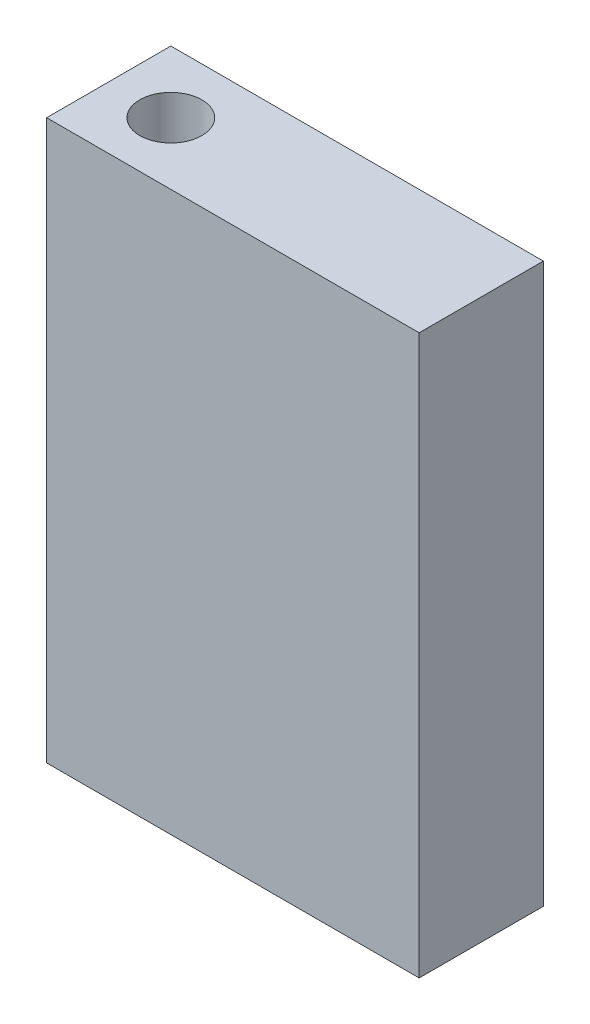
SolidWorks part; units mm, degrees
ref_plane "Front Plane" through (0, 0, 0) normal (0, 0, 1) x (1, 0, 0)
ref_plane "Top Plane" through (0, 0, 0) normal (0, 1, 0) x (1, 0, 0)
ref_plane "Right Plane" through (0, 0, 0) normal (1, 0, 0) x (0, 0, -1)
sketch "Sketch1" plane through (0, 0, 0) normal (0, 1, 0) x (1, 0, 0)
  line L1 (-23.0207, 17.3303) -> (6.9793, 17.3303)
  line L2 (-23.0207, 17.3303) -> (-23.0207, 27.3303)
  line L3 (-23.0207, 27.3303) -> (6.9793, 27.3303)
  line L4 (6.9793, 17.3303) -> (6.9793, 27.3303)
  dimension "D1" = 10
  dimension "D2" = 30
extrude "Boss-Extrude1" add sketch "Sketch1" along normal blind 45
sketch "Sketch2" plane through (0, 45, 0) normal (0, 1, 0) x (1, 0, 0)
  line L0 (6.9793, 17.3303) -> (6.9793, 27.3303) construction
  line L1 (6.9793, 27.3303) -> (-23.0207, 27.3303) construction
  circle A0 centre (-18.0207, 22.3303) radius 2.5
  dimension "D1" = 5
  dimension "D2" = 25
  dimension "D3" = 5
extrude "Cut-Extrude1" cut sketch "Sketch2" against normal blind 35
